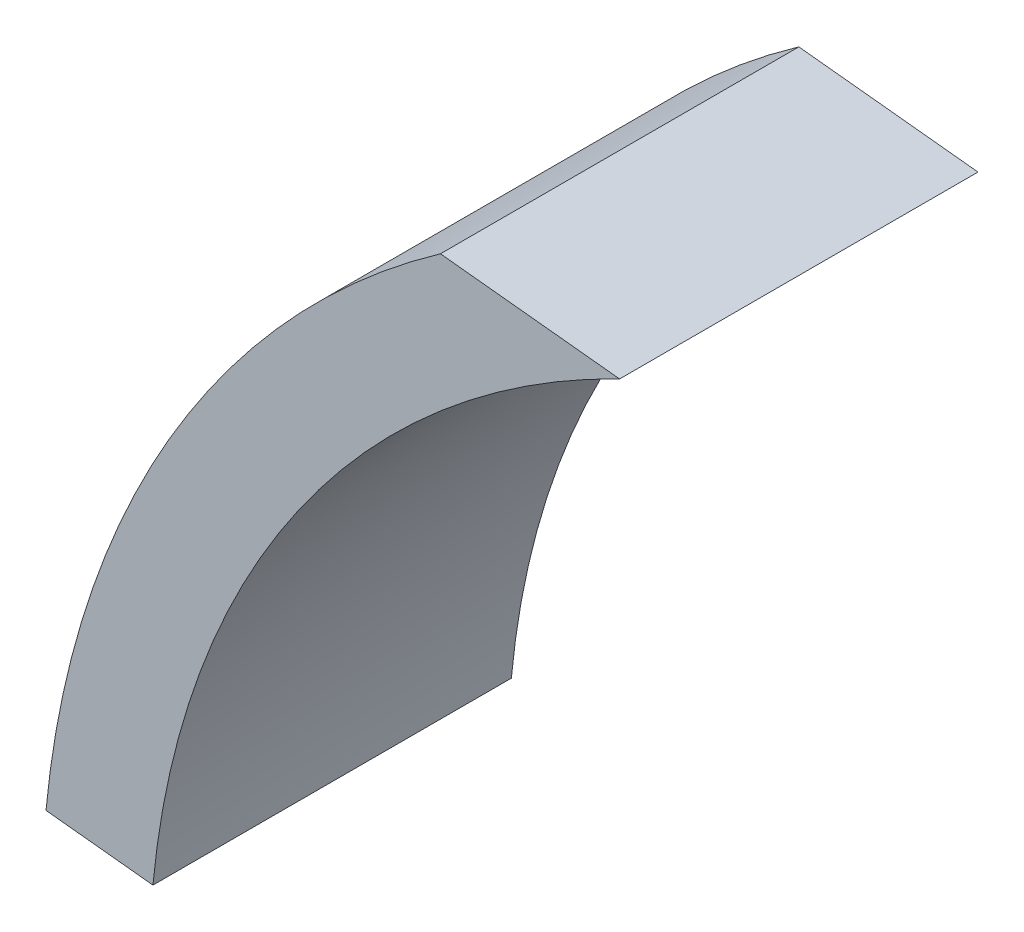
SolidWorks part; units mm, degrees
ref_plane "前视基准面" through (0, 0, 0) normal (0, 0, 1) x (1, 0, 0)
ref_plane "上视基准面" through (0, 0, 0) normal (0, 1, 0) x (1, 0, 0)
ref_plane "右视基准面" through (0, 0, 0) normal (1, 0, 0) x (0, 0, -1)
other "Configuration Table"
sketch "草图1" plane through (0, 0, 0) normal (0, 0, 1) x (1, 0, 0)
  line L0 (-9.3, 0) -> (-10.5, 0)
  line L1 (0, 0) -> (5.25, 0) construction
  line L2 (0, 0) -> (10.4425, 1.0975) construction
  line L3 (10.4425, 1.0975) -> (9.2491, 0.9721)
  arc A0 (9.2491, 0.9721) -> (-9.3, 0) centre (0, 0) ccw
  arc A1 (10.4425, 1.0975) -> (-10.5, 0) centre (0, 0) ccw
  dimension "D1" = 18.6
  dimension "D2" = 21
  dimension "D3" = 6
extrude "凸台-拉伸1" add sketch "草图1" along normal blind 6.15
sketch "草图2" plane through (0, 0, 6.15) normal (0, 0, 1) x (1, 0, 0)
  line L0 (0, 0) -> (4.6729, 0)
  line L1 (0, 0) -> (9.2491, 0.9721)
  line L2 (0, 0) -> (-9.3, 0)
  line L3 (0, 0) -> (-9.2491, 0.9721)
  arc A0 (9.2491, 0.9721) -> (-9.3, 0) centre (0, 0) ccw construction
  point P11 (0, 0)
  point P12 (0, 0)
  point P13 (0, 0)
  dimension "D1" = 6
ref_plane "基准面1" through (0, 0, 6.15) normal (0.9945, 0.1045, 0) x (0, 0, -1)
ref_plane "基准面2" through (0, 0, 6.15) normal (-0.9945, 0.1045, 0) x (0, 0, 1)
sketch "草图4" plane through (0, 0, 6.15) normal (-0.9945, 0.1045, 0) x (0, 0, 1)
  line L1 (0, -0.0975) -> (-4, -0.0975)
  line L3 (0, 7.9025) -> (-4, 7.9025)
  line L4 (-4, -0.0975) -> (-4, 7.9025)
  line L7 (0, -1.0975) -> (-6.15, -1.0975) construction
  line L8 (0, 7.9025) -> (0, 10.5)
  line L9 (0, -1.0975) -> (-6.15, -1.0975)
  line L10 (0, -1.0975) -> (0, -0.0975)
  line L11 (0, 10.5) -> (-6.15, 10.5)
  line L12 (-6.15, -1.0975) -> (-6.15, 10.5)
  dimension "D1" = 1
  dimension "D2" = 8
  dimension "D3" = 4
extrude "切除-拉伸1" cut sketch "草图4" against normal through all both and the other way through all
